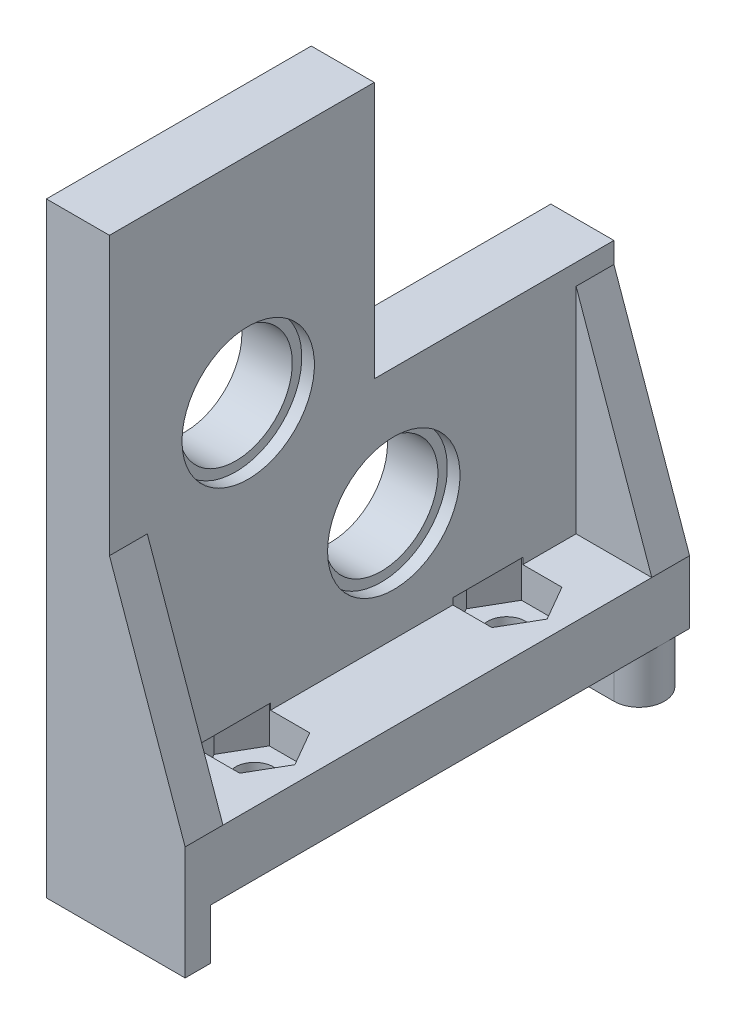
SolidWorks part; units mm, degrees
material "1060 合金"
ref_plane "前视基准面" through (0, 0, 0) normal (0, 0, 1) x (1, 0, 0)
ref_plane "上视基准面" through (0, 0, 0) normal (0, 1, 0) x (1, 0, 0)
ref_plane "右视基准面" through (0, 0, 0) normal (1, 0, 0) x (0, 0, -1)
sketch "草图1" plane through (0, 0, 0) normal (1, 0, 0) x (0, 0, -1)
  line L1 (-11, 17) -> (29, 17)
  line L2 (-11, 17) -> (-11, -27)
  line L3 (-11, -27) -> (29, -27)
  line L4 (29, 17) -> (29, -27)
  circle A6 centre (0, 0) radius 4.5
  circle A7 centre (18, 6) radius 4.5
  circle A8 centre (11.5439, -13.3514) radius 4.5
  dimension "D1" = 20.4
  dimension "D2" = 18.9737
  dimension "D3" = 17.65
  dimension "D4" = 9
  dimension "D5" = 9
  dimension "D7" = 11
  dimension "D6" = 11
  dimension "D8" = 18
  dimension "D9" = 27
  dimension "D10" = 11
extrude "凸台-拉伸1" add sketch "草图1" along normal blind 5
sketch "草图2" plane through (5, 0, 0) normal (-1, 0, 0) x (0, 0, 1)
  circle A0 centre (-18, 6) radius 5.25
  circle A1 centre (0, 0) radius 5.25
  circle A2 centre (-11.5439, -13.3514) radius 5.25
extrude "切除-拉伸1" cut sketch "草图2" along normal blind 1
sketch "草图3" plane through (5, 0, 0) normal (1, 0, 0) x (0, 0, -1)
  line L1 (29, 17) -> (10, 17)
  line L2 (29, 17) -> (29, -3.3514)
  line L3 (29, -3.3514) -> (10, -3.3514)
  line L4 (10, 17) -> (10, -3.3514)
  circle A0 centre (11.5439, -13.3514) radius 4.5 construction
  dimension "D1" = 10
  dimension "D2" = 10
extrude "切除-拉伸2" cut sketch "草图3" against normal up to next
sketch "草图4" plane through (5, 0, 0) normal (1, 0, 0) x (0, 0, -1)
  line L0 (29, -27) -> (29, -3.3514) construction
  line L1 (-11, -27) -> (29, -27)
  line L2 (-11, -27) -> (-11, -22)
  line L3 (-11, -22) -> (29, -22)
  line L4 (29, -27) -> (29, -22)
  dimension "D1" = 5
extrude "凸台-拉伸2" add sketch "草图4" along normal blind 6
sketch "草图5" plane through (0, -27, 0) normal (0, -1, 0) x (1, 0, 0)
  line L0 (0, 11) -> (11, 11)
  line L1 (8.8, 9) -> (5.5, 6)
  line L2 (5.5, 6) -> (2.2, 9)
  line L3 (0, 11) -> (0, 9)
  line L4 (0, -29) -> (9, -29)
  line L5 (0, -29) -> (0, -25)
  line L6 (0, -25) -> (9, -25)
  line L7 (11, -29) -> (0, -29) construction
  line L8 (0, 11) -> (0, -29) construction
  line L9 (0, 9) -> (2.2, 9)
  line L10 (11, 11) -> (11, -29) construction
  line L11 (11, 9) -> (11, 11)
  line L12 (8.8, 9) -> (11, 9)
  arc A0 (9, -25) -> (9, -29) centre (9, -27) cw
  dimension "D1" = 5
  dimension "D2" = 4
  dimension "D3" = 9
  dimension "D4" = 9
  dimension "D5" = 2
extrude "凸台-拉伸3" add sketch "草图5" along normal blind 4
sketch "草图6" plane through (0, -27, 0) normal (0, -1, 0) x (1, 0, 0)
  line L0 (0, 9) -> (0, -25) construction
  line L1 (9, -25) -> (0, -25) construction
  circle A0 centre (6.5, -19) radius 1.5
  circle A1 centre (6.5, 1) radius 1.5
  dimension "D3" = 3
  dimension "D4" = 3
  dimension "D1" = 6.5
  dimension "D2" = 6.5
  dimension "D5" = 6
  dimension "D6" = 5
extrude "切除-拉伸4" cut sketch "草图6" against normal blind 5
sketch "草图7" plane through (0, -22, 0) normal (0, 1, 0) x (-1, 0, 0)
  line L1 (-9.7043, -19) -> (-8.1021, -21.775)
  line L2 (-8.1021, -21.775) -> (-4.8979, -21.775)
  line L3 (-4.8979, -21.775) -> (-3.2957, -19)
  line L4 (-3.2957, -19) -> (-4.8979, -16.225)
  line L5 (-4.8979, -16.225) -> (-8.1021, -16.225)
  line L6 (-8.1021, -16.225) -> (-9.7043, -19)
  line L7 (-9.7043, 1) -> (-8.1021, -1.775)
  line L8 (-8.1021, -1.775) -> (-4.8979, -1.775)
  line L9 (-4.8979, -1.775) -> (-3.2957, 1)
  line L10 (-3.2957, 1) -> (-4.8979, 3.775)
  line L11 (-4.8979, 3.775) -> (-8.1021, 3.775)
  line L12 (-8.1021, 3.775) -> (-9.7043, 1)
  circle A0 centre (-6.5, -19) radius 2.775 construction
  circle A1 centre (-6.5, 1) radius 2.775 construction
  dimension "D1" = 5.55
  dimension "D2" = 5.55
extrude "切除-拉伸5" cut sketch "草图7" against normal blind 2.5 and the other way blind 0.5
sketch "草图8" plane through (0, 0, 11) normal (0, 0, 1) x (1, 0, 0)
  line L0 (5, -22) -> (11, -22)
  line L1 (11, -22) -> (5, -5)
  line L2 (5, 17) -> (5, -22) construction
  line L3 (5, -5) -> (5, -22)
  dimension "D1" = 17
extrude "凸台-拉伸4" add sketch "草图8" against normal blind 3
sketch "草图9" plane through (0, 0, -29) normal (0, 0, -1) x (-1, 0, 0)
  line L0 (-5, -22) -> (-11, -22)
  line L1 (-11, -22) -> (-5, -5)
  line L2 (-5, -22) -> (-5, -3.3514) construction
  line L3 (-5, -5) -> (-5, -22)
  dimension "D1" = 17
extrude "凸台-拉伸5" add sketch "草图9" against normal blind 3
